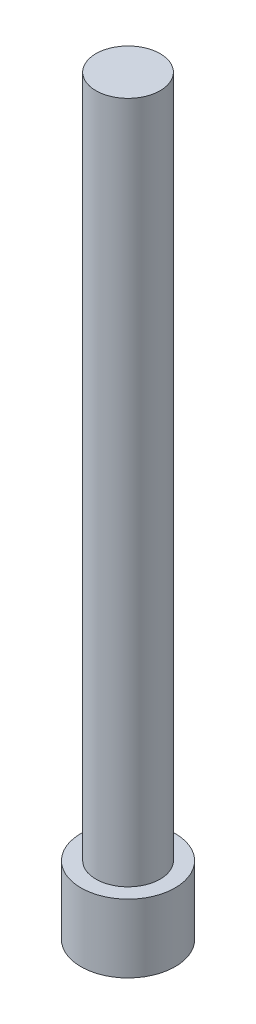
SolidWorks part; units mm, degrees
ref_plane "Front Plane" through (0, 0, 0) normal (0, 0, 1) x (1, 0, 0)
ref_plane "Top Plane" through (0, 0, 0) normal (0, 1, 0) x (1, 0, 0)
ref_plane "Right Plane" through (0, 0, 0) normal (1, 0, 0) x (0, 0, -1)
sketch "Sketch1" plane through (0, 0, 0) normal (0, 1, 0) x (1, 0, 0)
  circle A0 centre (0, 0) radius 2.35
  dimension "D1" = 4.7
extrude "Boss-Extrude1" add sketch "Sketch1" along normal blind 55
sketch "Sketch2" plane through (0, 0, 0) normal (0, -1, 0) x (1, 0, 0)
  circle A0 centre (0, 0) radius 3.45
  circle A1 centre (0, 0) radius 2.35
  circle A2 centre (0, 0) radius 2.35
  dimension "D1" = 0
  dimension "D2" = 1.1
extrude "Boss-Extrude2" add sketch "Sketch2" against normal blind 5
